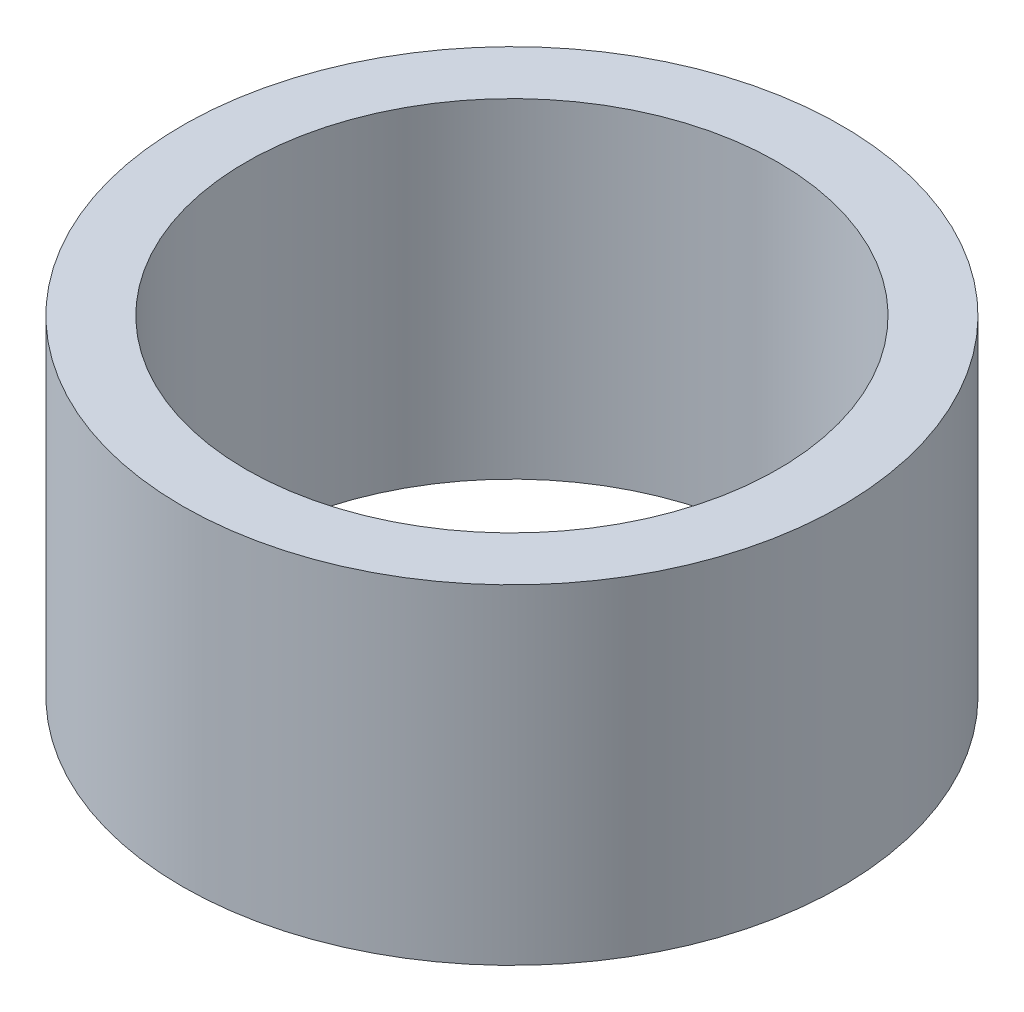
SolidWorks part; units mm, degrees
ref_plane "前视基准面" through (0, 0, 0) normal (0, 0, 1) x (1, 0, 0)
ref_plane "上视基准面" through (0, 0, 0) normal (0, 1, 0) x (1, 0, 0)
ref_plane "右视基准面" through (0, 0, 0) normal (1, 0, 0) x (0, 0, -1)
sketch "草图1" plane through (0, 0, 0) normal (0, 0, 1) x (1, 0, 0)
  line L0 (0, 161.3762) -> (0, 0) construction
  line L1 (141.7365, 0) -> (-131.7984, 0) construction
  line L2 (25.4, 0) -> (25.4, 25.4)
  line L3 (20.5, 25.4) -> (25.4, 25.4)
  line L4 (20.5, 0) -> (25.4, 0)
  line L7 (20.5, 25.4) -> (20.5, 0)
  dimension "D2" = 25.4
  dimension "D3" = 25.4
  dimension "D11" = 20.5
revolve "旋转1" add sketch "草图1" angle 360 about L0
cosmetic thread "装饰螺纹线1" parameters "D2"=42
